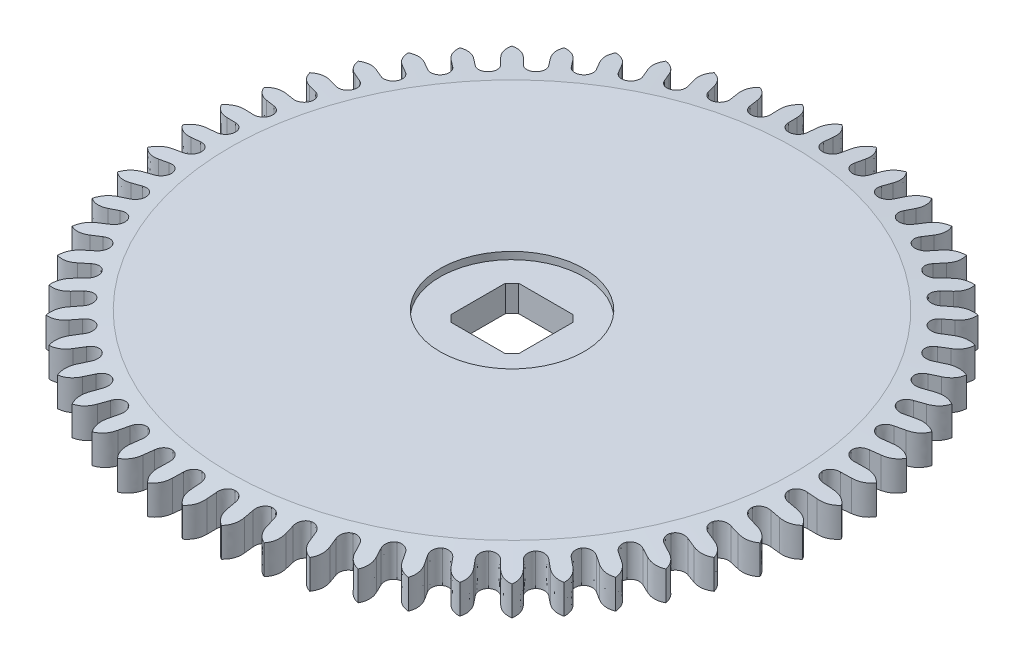
SolidWorks part; units mm, degrees
ref_plane "Alzado" through (0, 0, 0) normal (0, 0, 1) x (1, 0, 0)
ref_plane "Planta" through (0, 0, 0) normal (0, 1, 0) x (1, 0, 0)
ref_plane "Vista lateral" through (0, 0, 0) normal (1, 0, 0) x (0, 0, -1)
sketch "Sketch2" plane through (0, 0, 0) normal (0, 1, 0) x (1, 0, 0)
  circle A0 centre (0, 0) radius 6.875
  dimension "D1" = 13.75
extrude "Boss-Extrude2" add sketch "Sketch2" along normal blind 0.7
chamfer "Chamfer1" distance 0.09 distance2 1 1 edges at (0, 0.7, 6.875)
sketch "Sketch1" plane through (0, 0, 0) normal (0, 1, 0) x (1, 0, 0)
  line L0 (0, -1000) -> (0, 49000) construction
  line L1 (0, 0) -> (2803.5223, 49921.3408) construction
  line L2 (0.167, 6.5259) -> (0.167, 6.3258)
  line L3 (0.167, -994.7938) -> (0.167, 49005.2062) construction
  line L4 (-0.167, 6.5259) -> (-0.167, 6.3258)
  line L5 (0.5647, 6.5035) -> (0.5423, 6.3047)
  line L6 (0.8966, 6.4661) -> (0.8742, 6.2673)
  line L7 (1.2893, 6.3994) -> (1.2448, 6.2044)
  line L8 (1.615, 6.3251) -> (1.5704, 6.13)
  line L9 (1.9977, 6.2148) -> (1.9316, 6.026)
  line L10 (2.313, 6.1045) -> (2.2469, 5.9157)
  line L11 (2.681, 5.9521) -> (2.5942, 5.7718)
  line L12 (2.9819, 5.8071) -> (2.8951, 5.6269)
  line L13 (3.3306, 5.6145) -> (3.2241, 5.4451)
  line L14 (3.6134, 5.4368) -> (3.5069, 5.2674)
  line L15 (3.9382, 5.2062) -> (3.8135, 5.0498)
  line L16 (4.1994, 4.998) -> (4.0746, 4.8416)
  line L17 (4.4964, 4.7326) -> (4.3549, 4.5911)
  line L18 (4.7326, 4.4964) -> (4.5911, 4.3549)
  line L19 (4.998, 4.1994) -> (4.8416, 4.0746)
  line L20 (5.2062, 3.9382) -> (5.0498, 3.8135)
  line L21 (5.4368, 3.6134) -> (5.2674, 3.5069)
  line L22 (5.6145, 3.3306) -> (5.4451, 3.2241)
  line L23 (5.8071, 2.9819) -> (5.6269, 2.8951)
  line L24 (5.9521, 2.681) -> (5.7718, 2.5942)
  line L25 (6.1045, 2.313) -> (5.9157, 2.2469)
  line L26 (6.2148, 1.9977) -> (6.026, 1.9316)
  line L27 (6.3251, 1.615) -> (6.13, 1.5704)
  line L28 (6.3994, 1.2893) -> (6.2044, 1.2448)
  line L29 (6.4661, 0.8966) -> (6.2673, 0.8742)
  line L30 (6.5035, 0.5647) -> (6.3047, 0.5423)
  line L31 (6.5259, 0.167) -> (6.3258, 0.167)
  line L32 (6.5259, -0.167) -> (6.3258, -0.167)
  line L33 (6.5035, -0.5647) -> (6.3047, -0.5423)
  line L34 (6.4661, -0.8966) -> (6.2673, -0.8742)
  line L35 (6.3994, -1.2893) -> (6.2044, -1.2448)
  line L36 (6.3251, -1.615) -> (6.13, -1.5704)
  line L37 (6.2148, -1.9977) -> (6.026, -1.9316)
  line L38 (6.1045, -2.313) -> (5.9157, -2.2469)
  line L39 (5.9521, -2.681) -> (5.7718, -2.5942)
  line L40 (5.8071, -2.9819) -> (5.6269, -2.8951)
  line L41 (5.6145, -3.3306) -> (5.4451, -3.2241)
  line L42 (5.4368, -3.6134) -> (5.2674, -3.5069)
  line L43 (5.2062, -3.9382) -> (5.0498, -3.8135)
  line L44 (4.998, -4.1994) -> (4.8416, -4.0746)
  line L45 (4.7326, -4.4964) -> (4.5911, -4.3549)
  line L46 (4.4964, -4.7326) -> (4.3549, -4.5911)
  line L47 (4.1994, -4.998) -> (4.0746, -4.8416)
  line L48 (3.9382, -5.2062) -> (3.8135, -5.0498)
  line L49 (3.6134, -5.4368) -> (3.5069, -5.2674)
  line L50 (3.3306, -5.6145) -> (3.2241, -5.4451)
  line L51 (2.9819, -5.8071) -> (2.8951, -5.6269)
  line L52 (2.681, -5.9521) -> (2.5942, -5.7718)
  line L53 (2.313, -6.1045) -> (2.2469, -5.9157)
  line L54 (1.9977, -6.2148) -> (1.9316, -6.026)
  line L55 (1.615, -6.3251) -> (1.5704, -6.13)
  line L56 (1.2893, -6.3994) -> (1.2448, -6.2044)
  line L57 (0.8966, -6.4661) -> (0.8742, -6.2673)
  line L58 (0.5647, -6.5035) -> (0.5423, -6.3047)
  line L59 (0.167, -6.5259) -> (0.167, -6.3258)
  line L60 (-0.167, -6.5259) -> (-0.167, -6.3258)
  line L61 (-0.5647, -6.5035) -> (-0.5423, -6.3047)
  line L62 (-0.8966, -6.4661) -> (-0.8742, -6.2673)
  line L63 (-1.2893, -6.3994) -> (-1.2448, -6.2044)
  line L64 (-1.615, -6.3251) -> (-1.5704, -6.13)
  line L65 (-1.9977, -6.2148) -> (-1.9316, -6.026)
  line L66 (-2.313, -6.1045) -> (-2.2469, -5.9157)
  line L67 (-2.681, -5.9521) -> (-2.5942, -5.7718)
  line L68 (-2.9819, -5.8071) -> (-2.8951, -5.6269)
  line L69 (-3.3306, -5.6145) -> (-3.2241, -5.4451)
  line L70 (-3.6134, -5.4368) -> (-3.5069, -5.2674)
  line L71 (-3.9382, -5.2062) -> (-3.8135, -5.0498)
  line L72 (-4.1994, -4.998) -> (-4.0746, -4.8416)
  line L73 (-4.4964, -4.7326) -> (-4.3549, -4.5911)
  line L74 (-4.7326, -4.4964) -> (-4.5911, -4.3549)
  line L75 (-4.998, -4.1994) -> (-4.8416, -4.0746)
  line L76 (-5.2062, -3.9382) -> (-5.0498, -3.8135)
  line L77 (-5.4368, -3.6134) -> (-5.2674, -3.5069)
  line L78 (-5.6145, -3.3306) -> (-5.4451, -3.2241)
  line L79 (-5.8071, -2.9819) -> (-5.6269, -2.8951)
  line L80 (-5.9521, -2.681) -> (-5.7718, -2.5942)
  line L81 (-6.1045, -2.313) -> (-5.9157, -2.2469)
  line L82 (-6.2148, -1.9977) -> (-6.026, -1.9316)
  line L83 (-6.3251, -1.615) -> (-6.13, -1.5704)
  line L84 (-6.3994, -1.2893) -> (-6.2044, -1.2448)
  line L85 (-6.4661, -0.8966) -> (-6.2673, -0.8742)
  line L86 (-6.5035, -0.5647) -> (-6.3047, -0.5423)
  line L87 (-6.5259, -0.167) -> (-6.3258, -0.167)
  line L88 (-6.5259, 0.167) -> (-6.3258, 0.167)
  line L89 (-6.5035, 0.5647) -> (-6.3047, 0.5423)
  line L90 (-6.4661, 0.8966) -> (-6.2673, 0.8742)
  line L91 (-6.3994, 1.2893) -> (-6.2044, 1.2448)
  line L92 (-6.3251, 1.615) -> (-6.13, 1.5704)
  line L93 (-6.2148, 1.9977) -> (-6.026, 1.9316)
  line L94 (-6.1045, 2.313) -> (-5.9157, 2.2469)
  line L95 (-5.9521, 2.681) -> (-5.7718, 2.5942)
  line L96 (-5.8071, 2.9819) -> (-5.6269, 2.8951)
  line L97 (-5.6145, 3.3306) -> (-5.4451, 3.2241)
  line L98 (-5.4368, 3.6134) -> (-5.2674, 3.5069)
  line L99 (-5.2062, 3.9382) -> (-5.0498, 3.8135)
  line L100 (-4.998, 4.1994) -> (-4.8416, 4.0746)
  line L101 (-4.7326, 4.4964) -> (-4.5911, 4.3549)
  line L102 (-4.4964, 4.7326) -> (-4.3549, 4.5911)
  line L103 (-4.1994, 4.998) -> (-4.0746, 4.8416)
  line L104 (-3.9382, 5.2062) -> (-3.8135, 5.0498)
  line L105 (-3.6134, 5.4368) -> (-3.5069, 5.2674)
  line L106 (-3.3306, 5.6145) -> (-3.2241, 5.4451)
  line L107 (-2.9819, 5.8071) -> (-2.8951, 5.6269)
  line L108 (-2.681, 5.9521) -> (-2.5942, 5.7718)
  line L109 (-2.313, 6.1045) -> (-2.2469, 5.9157)
  line L110 (-1.9977, 6.2148) -> (-1.9316, 6.026)
  line L111 (-1.615, 6.3251) -> (-1.5704, 6.13)
  line L112 (-1.2893, 6.3994) -> (-1.2448, 6.2044)
  line L113 (-0.8966, 6.4661) -> (-0.8742, 6.2673)
  line L114 (-0.5647, 6.5035) -> (-0.5423, 6.3047)
  circle A0 centre (0, 0) radius 6.875 construction
  circle A1 centre (0, 0) radius 6.125 construction
  circle A2 centre (0, 0) radius 6.328 construction
  circle A3 centre (0, 0) radius 6.528 construction
  parabola Q0 (0, 6.875) -> (0.167, 6.5259) focus (-0.047, 6.652) apex (0.118, 6.742)
  parabola Q1 (0, 6.875) -> (-0.167, 6.5259) focus (0.047, 6.652) apex (-0.118, 6.742)
  parabola Q2 (0.7686, 6.8218) -> (0.5647, 6.5035) focus (0.7904, 6.595) apex (0.6364, 6.7028)
  parabola Q3 (0.7686, 6.8218) -> (0.8966, 6.4661) focus (0.697, 6.6055) apex (0.871, 6.6764)
  parabola Q4 (1.5276, 6.6929) -> (1.2893, 6.3994) focus (1.5238, 6.465) apex (1.3829, 6.5894)
  parabola Q5 (1.5276, 6.6929) -> (1.615, 6.3251) focus (1.4322, 6.4859) apex (1.6131, 6.5369)
  parabola Q6 (2.2674, 6.4798) -> (1.9977, 6.2148) focus (2.2381, 6.2537) apex (2.112, 6.3931)
  parabola Q7 (2.2674, 6.4798) -> (2.313, 6.1045) focus (2.1494, 6.2848) apex (2.3348, 6.3151)
  parabola Q8 (2.9786, 6.1852) -> (2.681, 5.9521) focus (2.9242, 5.9638) apex (2.8145, 6.1164)
  parabola Q9 (2.9786, 6.1852) -> (2.9819, 5.8071) focus (2.8395, 6.0046) apex (3.0272, 6.014)
  parabola Q10 (3.6524, 5.8128) -> (3.3306, 5.6145) focus (3.5736, 5.5989) apex (3.4816, 5.7629)
  parabola Q11 (3.6524, 5.8128) -> (3.6134, 5.4368) focus (3.494, 5.6489) apex (3.6815, 5.6373)
  parabola Q12 (4.2803, 5.3673) -> (3.9382, 5.2062) focus (4.178, 5.1636) apex (4.105, 5.3368)
  parabola Q13 (4.2803, 5.3673) -> (4.1994, 4.998) focus (4.1045, 5.2222) apex (4.2895, 5.1896)
  parabola Q14 (4.8543, 4.8543) -> (4.4964, 4.7326) focus (4.7298, 4.6634) apex (4.6767, 4.8436)
  parabola Q15 (4.8543, 4.8543) -> (4.7326, 4.4964) focus (4.6634, 4.7298) apex (4.8436, 4.6767)
  parabola Q16 (5.3673, 4.2803) -> (4.998, 4.1994) focus (5.2222, 4.1045) apex (5.1896, 4.2895)
  parabola Q17 (5.3673, 4.2803) -> (5.2062, 3.9382) focus (5.1636, 4.178) apex (5.3368, 4.105)
  parabola Q18 (5.8128, 3.6524) -> (5.4368, 3.6134) focus (5.6489, 3.494) apex (5.6373, 3.6815)
  parabola Q19 (5.8128, 3.6524) -> (5.6145, 3.3306) focus (5.5989, 3.5736) apex (5.7629, 3.4816)
  parabola Q20 (6.1852, 2.9786) -> (5.8071, 2.9819) focus (6.0046, 2.8395) apex (6.014, 3.0272)
  parabola Q21 (6.1852, 2.9786) -> (5.9521, 2.681) focus (5.9638, 2.9242) apex (6.1164, 2.8145)
  parabola Q22 (6.4798, 2.2674) -> (6.1045, 2.313) focus (6.2848, 2.1494) apex (6.3151, 2.3348)
  parabola Q23 (6.4798, 2.2674) -> (6.2148, 1.9977) focus (6.2537, 2.2381) apex (6.3931, 2.112)
  parabola Q24 (6.6929, 1.5276) -> (6.3251, 1.615) focus (6.4859, 1.4322) apex (6.5369, 1.6131)
  parabola Q25 (6.6929, 1.5276) -> (6.3994, 1.2893) focus (6.465, 1.5238) apex (6.5894, 1.3829)
  parabola Q26 (6.8218, 0.7686) -> (6.4661, 0.8966) focus (6.6055, 0.697) apex (6.6764, 0.871)
  parabola Q27 (6.8218, 0.7686) -> (6.5035, 0.5647) focus (6.595, 0.7904) apex (6.7028, 0.6364)
  parabola Q28 (6.865, 0) -> (6.5259, 0.167) focus (6.642, -0.047) apex (6.7319, 0.118)
  parabola Q29 (6.865, 0) -> (6.5259, -0.167) focus (6.642, 0.047) apex (6.7319, -0.118)
  parabola Q30 (6.8218, -0.7686) -> (6.5035, -0.5647) focus (6.595, -0.7904) apex (6.7028, -0.6364)
  parabola Q31 (6.8218, -0.7686) -> (6.4661, -0.8966) focus (6.6055, -0.697) apex (6.6764, -0.871)
  parabola Q32 (6.6929, -1.5276) -> (6.3994, -1.2893) focus (6.465, -1.5238) apex (6.5894, -1.3829)
  parabola Q33 (6.6929, -1.5276) -> (6.3251, -1.615) focus (6.4859, -1.4322) apex (6.5369, -1.6131)
  parabola Q34 (6.4798, -2.2674) -> (6.2148, -1.9977) focus (6.2537, -2.2381) apex (6.3931, -2.112)
  parabola Q35 (6.4798, -2.2674) -> (6.1045, -2.313) focus (6.2848, -2.1494) apex (6.3151, -2.3348)
  parabola Q36 (6.1852, -2.9786) -> (5.9521, -2.681) focus (5.9638, -2.9242) apex (6.1164, -2.8145)
  parabola Q37 (6.1852, -2.9786) -> (5.8071, -2.9819) focus (6.0046, -2.8395) apex (6.014, -3.0272)
  parabola Q38 (5.8128, -3.6524) -> (5.6145, -3.3306) focus (5.5989, -3.5736) apex (5.7629, -3.4816)
  parabola Q39 (5.8128, -3.6524) -> (5.4368, -3.6134) focus (5.6489, -3.494) apex (5.6373, -3.6815)
  parabola Q40 (5.3673, -4.2803) -> (5.2062, -3.9382) focus (5.1636, -4.178) apex (5.3368, -4.105)
  parabola Q41 (5.3673, -4.2803) -> (4.998, -4.1994) focus (5.2222, -4.1045) apex (5.1896, -4.2895)
  parabola Q42 (4.8543, -4.8543) -> (4.7326, -4.4964) focus (4.6634, -4.7298) apex (4.8436, -4.6767)
  parabola Q43 (4.8543, -4.8543) -> (4.4964, -4.7326) focus (4.7298, -4.6634) apex (4.6767, -4.8436)
  parabola Q44 (4.2803, -5.3673) -> (4.1994, -4.998) focus (4.1045, -5.2222) apex (4.2895, -5.1896)
  parabola Q45 (4.2803, -5.3673) -> (3.9382, -5.2062) focus (4.178, -5.1636) apex (4.105, -5.3368)
  parabola Q46 (3.6524, -5.8128) -> (3.6134, -5.4368) focus (3.494, -5.6489) apex (3.6815, -5.6373)
  parabola Q47 (3.6524, -5.8128) -> (3.3306, -5.6145) focus (3.5736, -5.5989) apex (3.4816, -5.7629)
  parabola Q48 (2.9786, -6.1852) -> (2.9819, -5.8071) focus (2.8395, -6.0046) apex (3.0272, -6.014)
  parabola Q49 (2.9786, -6.1852) -> (2.681, -5.9521) focus (2.9242, -5.9638) apex (2.8145, -6.1164)
  parabola Q50 (2.2674, -6.4798) -> (2.313, -6.1045) focus (2.1494, -6.2848) apex (2.3348, -6.3151)
  parabola Q51 (2.2674, -6.4798) -> (1.9977, -6.2148) focus (2.2381, -6.2537) apex (2.112, -6.3931)
  parabola Q52 (1.5276, -6.6929) -> (1.615, -6.3251) focus (1.4322, -6.4859) apex (1.6131, -6.5369)
  parabola Q53 (1.5276, -6.6929) -> (1.2893, -6.3994) focus (1.5238, -6.465) apex (1.3829, -6.5894)
  parabola Q54 (0.7686, -6.8218) -> (0.8966, -6.4661) focus (0.697, -6.6055) apex (0.871, -6.6764)
  parabola Q55 (0.7686, -6.8218) -> (0.5647, -6.5035) focus (0.7904, -6.595) apex (0.6364, -6.7028)
  parabola Q56 (0, -6.865) -> (0.167, -6.5259) focus (-0.047, -6.642) apex (0.118, -6.7319)
  parabola Q57 (0, -6.865) -> (-0.167, -6.5259) focus (0.047, -6.642) apex (-0.118, -6.7319)
  parabola Q58 (-0.7686, -6.8218) -> (-0.5647, -6.5035) focus (-0.7904, -6.595) apex (-0.6364, -6.7028)
  parabola Q59 (-0.7686, -6.8218) -> (-0.8966, -6.4661) focus (-0.697, -6.6055) apex (-0.871, -6.6764)
  parabola Q60 (-1.5276, -6.6929) -> (-1.2893, -6.3994) focus (-1.5238, -6.465) apex (-1.3829, -6.5894)
  parabola Q61 (-1.5276, -6.6929) -> (-1.615, -6.3251) focus (-1.4322, -6.4859) apex (-1.6131, -6.5369)
  parabola Q62 (-2.2674, -6.4798) -> (-1.9977, -6.2148) focus (-2.2381, -6.2537) apex (-2.112, -6.3931)
  parabola Q63 (-2.2674, -6.4798) -> (-2.313, -6.1045) focus (-2.1494, -6.2848) apex (-2.3348, -6.3151)
  parabola Q64 (-2.9786, -6.1852) -> (-2.681, -5.9521) focus (-2.9242, -5.9638) apex (-2.8145, -6.1164)
  parabola Q65 (-2.9786, -6.1852) -> (-2.9819, -5.8071) focus (-2.8395, -6.0046) apex (-3.0272, -6.014)
  parabola Q66 (-3.6524, -5.8128) -> (-3.3306, -5.6145) focus (-3.5736, -5.5989) apex (-3.4816, -5.7629)
  parabola Q67 (-3.6524, -5.8128) -> (-3.6134, -5.4368) focus (-3.494, -5.6489) apex (-3.6815, -5.6373)
  parabola Q68 (-4.2803, -5.3673) -> (-3.9382, -5.2062) focus (-4.178, -5.1636) apex (-4.105, -5.3368)
  parabola Q69 (-4.2803, -5.3673) -> (-4.1994, -4.998) focus (-4.1045, -5.2222) apex (-4.2895, -5.1896)
  parabola Q70 (-4.8543, -4.8543) -> (-4.4964, -4.7326) focus (-4.7298, -4.6634) apex (-4.6767, -4.8436)
  parabola Q71 (-4.8543, -4.8543) -> (-4.7326, -4.4964) focus (-4.6634, -4.7298) apex (-4.8436, -4.6767)
  parabola Q72 (-5.3673, -4.2803) -> (-4.998, -4.1994) focus (-5.2222, -4.1045) apex (-5.1896, -4.2895)
  parabola Q73 (-5.3673, -4.2803) -> (-5.2062, -3.9382) focus (-5.1636, -4.178) apex (-5.3368, -4.105)
  parabola Q74 (-5.8128, -3.6524) -> (-5.4368, -3.6134) focus (-5.6489, -3.494) apex (-5.6373, -3.6815)
  parabola Q75 (-5.8128, -3.6524) -> (-5.6145, -3.3306) focus (-5.5989, -3.5736) apex (-5.7629, -3.4816)
  parabola Q76 (-6.1852, -2.9786) -> (-5.8071, -2.9819) focus (-6.0046, -2.8395) apex (-6.014, -3.0272)
  parabola Q77 (-6.1852, -2.9786) -> (-5.9521, -2.681) focus (-5.9638, -2.9242) apex (-6.1164, -2.8145)
  parabola Q78 (-6.4798, -2.2674) -> (-6.1045, -2.313) focus (-6.2848, -2.1494) apex (-6.3151, -2.3348)
  parabola Q79 (-6.4798, -2.2674) -> (-6.2148, -1.9977) focus (-6.2537, -2.2381) apex (-6.3931, -2.112)
  parabola Q80 (-6.6929, -1.5276) -> (-6.3251, -1.615) focus (-6.4859, -1.4322) apex (-6.5369, -1.6131)
  parabola Q81 (-6.6929, -1.5276) -> (-6.3994, -1.2893) focus (-6.465, -1.5238) apex (-6.5894, -1.3829)
  parabola Q82 (-6.8218, -0.7686) -> (-6.4661, -0.8966) focus (-6.6055, -0.697) apex (-6.6764, -0.871)
  parabola Q83 (-6.8218, -0.7686) -> (-6.5035, -0.5647) focus (-6.595, -0.7904) apex (-6.7028, -0.6364)
  parabola Q84 (-6.865, 0) -> (-6.5259, -0.167) focus (-6.642, 0.047) apex (-6.7319, -0.118)
  parabola Q85 (-6.865, 0) -> (-6.5259, 0.167) focus (-6.642, -0.047) apex (-6.7319, 0.118)
  parabola Q86 (-6.8218, 0.7686) -> (-6.5035, 0.5647) focus (-6.595, 0.7904) apex (-6.7028, 0.6364)
  parabola Q87 (-6.8218, 0.7686) -> (-6.4661, 0.8966) focus (-6.6055, 0.697) apex (-6.6764, 0.871)
  parabola Q88 (-6.6929, 1.5276) -> (-6.3994, 1.2893) focus (-6.465, 1.5238) apex (-6.5894, 1.3829)
  parabola Q89 (-6.6929, 1.5276) -> (-6.3251, 1.615) focus (-6.4859, 1.4322) apex (-6.5369, 1.6131)
  parabola Q90 (-6.4798, 2.2674) -> (-6.2148, 1.9977) focus (-6.2537, 2.2381) apex (-6.3931, 2.112)
  parabola Q91 (-6.4798, 2.2674) -> (-6.1045, 2.313) focus (-6.2848, 2.1494) apex (-6.3151, 2.3348)
  parabola Q92 (-6.1852, 2.9786) -> (-5.9521, 2.681) focus (-5.9638, 2.9242) apex (-6.1164, 2.8145)
  parabola Q93 (-6.1852, 2.9786) -> (-5.8071, 2.9819) focus (-6.0046, 2.8395) apex (-6.014, 3.0272)
  parabola Q94 (-5.8128, 3.6524) -> (-5.6145, 3.3306) focus (-5.5989, 3.5736) apex (-5.7629, 3.4816)
  parabola Q95 (-5.8128, 3.6524) -> (-5.4368, 3.6134) focus (-5.6489, 3.494) apex (-5.6373, 3.6815)
  parabola Q96 (-5.3673, 4.2803) -> (-5.2062, 3.9382) focus (-5.1636, 4.178) apex (-5.3368, 4.105)
  parabola Q97 (-5.3673, 4.2803) -> (-4.998, 4.1994) focus (-5.2222, 4.1045) apex (-5.1896, 4.2895)
  parabola Q98 (-4.8543, 4.8543) -> (-4.7326, 4.4964) focus (-4.6634, 4.7298) apex (-4.8436, 4.6767)
  parabola Q99 (-4.8543, 4.8543) -> (-4.4964, 4.7326) focus (-4.7298, 4.6634) apex (-4.6767, 4.8436)
  parabola Q100 (-4.2803, 5.3673) -> (-4.1994, 4.998) focus (-4.1045, 5.2222) apex (-4.2895, 5.1896)
  parabola Q101 (-4.2803, 5.3673) -> (-3.9382, 5.2062) focus (-4.178, 5.1636) apex (-4.105, 5.3368)
  parabola Q102 (-3.6524, 5.8128) -> (-3.6134, 5.4368) focus (-3.494, 5.6489) apex (-3.6815, 5.6373)
  parabola Q103 (-3.6524, 5.8128) -> (-3.3306, 5.6145) focus (-3.5736, 5.5989) apex (-3.4816, 5.7629)
  parabola Q104 (-2.9786, 6.1852) -> (-2.9819, 5.8071) focus (-2.8395, 6.0046) apex (-3.0272, 6.014)
  parabola Q105 (-2.9786, 6.1852) -> (-2.681, 5.9521) focus (-2.9242, 5.9638) apex (-2.8145, 6.1164)
  parabola Q106 (-2.2674, 6.4798) -> (-2.313, 6.1045) focus (-2.1494, 6.2848) apex (-2.3348, 6.3151)
  parabola Q107 (-2.2674, 6.4798) -> (-1.9977, 6.2148) focus (-2.2381, 6.2537) apex (-2.112, 6.3931)
  parabola Q108 (-1.5276, 6.6929) -> (-1.615, 6.3251) focus (-1.4322, 6.4859) apex (-1.6131, 6.5369)
  parabola Q109 (-1.5276, 6.6929) -> (-1.2893, 6.3994) focus (-1.5238, 6.465) apex (-1.3829, 6.5894)
  parabola Q110 (-0.7686, 6.8218) -> (-0.8966, 6.4661) focus (-0.697, 6.6055) apex (-0.871, 6.6764)
  parabola Q111 (-0.7686, 6.8218) -> (-0.5647, 6.5035) focus (-0.7904, 6.595) apex (-0.6364, 6.7028)
  spline S0 degree 3 poles (0.167, 6.3258) (0.1637, 6.2132) (0.2418, 6.1215) (0.3434, 6.1154) knots 0 0 0 0 1 1 1 1
  spline S1 degree 3 poles (-0.167, 6.3258) (-0.1637, 6.2132) (-0.2418, 6.1215) (-0.3434, 6.1154) knots 0 0 0 0 1 1 1 1
  spline S2 degree 3 poles (0.5423, 6.3047) (0.533, 6.1925) (0.4451, 6.1101) (0.3434, 6.1154) knots 0 0 0 0 1 1 1 1
  spline S3 degree 3 poles (0.8742, 6.2673) (0.8583, 6.1558) (0.9257, 6.056) (1.026, 6.0385) knots 0 0 0 0 1 1 1 1
  spline S4 degree 3 poles (1.2448, 6.2044) (1.223, 6.0938) (1.1264, 6.0219) (1.026, 6.0385) knots 0 0 0 0 1 1 1 1
  spline S5 degree 3 poles (1.5704, 6.13) (1.5422, 6.021) (1.5979, 5.9143) (1.6956, 5.8856) knots 0 0 0 0 1 1 1 1
  spline S6 degree 3 poles (1.9316, 6.026) (1.8976, 5.9186) (1.7936, 5.8579) (1.6956, 5.8856) knots 0 0 0 0 1 1 1 1
  spline S7 degree 3 poles (2.2469, 5.9157) (2.2066, 5.8105) (2.2501, 5.6982) (2.3439, 5.6588) knots 0 0 0 0 1 1 1 1
  spline S8 degree 3 poles (2.5942, 5.7718) (2.5483, 5.6689) (2.4382, 5.6202) (2.3439, 5.6588) knots 0 0 0 0 1 1 1 1
  spline S9 degree 3 poles (2.8951, 5.6269) (2.8433, 5.5269) (2.8739, 5.4104) (2.9628, 5.3607) knots 0 0 0 0 1 1 1 1
  spline S10 degree 3 poles (3.2241, 5.4451) (3.167, 5.348) (3.0521, 5.3119) (2.9628, 5.3607) knots 0 0 0 0 1 1 1 1
  spline S11 degree 3 poles (3.5069, 5.2674) (3.4442, 5.1738) (3.4616, 5.0546) (3.5444, 4.9953) knots 0 0 0 0 1 1 1 1
  spline S12 degree 3 poles (3.8135, 5.0498) (3.7459, 4.9597) (3.6277, 4.9368) (3.5444, 4.9953) knots 0 0 0 0 1 1 1 1
  spline S13 degree 3 poles (4.0746, 4.8416) (4.0019, 4.7556) (4.0058, 4.6352) (4.0814, 4.5671) knots 0 0 0 0 1 1 1 1
  spline S14 degree 3 poles (4.3549, 4.5911) (4.2776, 4.5092) (4.1576, 4.4996) (4.0814, 4.5671) knots 0 0 0 0 1 1 1 1
  spline S15 degree 3 poles (4.5911, 4.3549) (4.5092, 4.2776) (4.4996, 4.1576) (4.5671, 4.0814) knots 0 0 0 0 1 1 1 1
  spline S16 degree 3 poles (4.8416, 4.0746) (4.7556, 4.0019) (4.6352, 4.0058) (4.5671, 4.0814) knots 0 0 0 0 1 1 1 1
  spline S17 degree 3 poles (5.0498, 3.8135) (4.9597, 3.7459) (4.9368, 3.6277) (4.9953, 3.5444) knots 0 0 0 0 1 1 1 1
  spline S18 degree 3 poles (5.2674, 3.5069) (5.1738, 3.4442) (5.0546, 3.4616) (4.9953, 3.5444) knots 0 0 0 0 1 1 1 1
  spline S19 degree 3 poles (5.4451, 3.2241) (5.348, 3.167) (5.3119, 3.0521) (5.3607, 2.9628) knots 0 0 0 0 1 1 1 1
  spline S20 degree 3 poles (5.6269, 2.8951) (5.5269, 2.8433) (5.4104, 2.8739) (5.3607, 2.9628) knots 0 0 0 0 1 1 1 1
  spline S21 degree 3 poles (5.7718, 2.5942) (5.6689, 2.5483) (5.6202, 2.4382) (5.6588, 2.3439) knots 0 0 0 0 1 1 1 1
  spline S22 degree 3 poles (5.9157, 2.2469) (5.8105, 2.2066) (5.6982, 2.2501) (5.6588, 2.3439) knots 0 0 0 0 1 1 1 1
  spline S23 degree 3 poles (6.026, 1.9316) (5.9186, 1.8976) (5.8579, 1.7936) (5.8856, 1.6956) knots 0 0 0 0 1 1 1 1
  spline S24 degree 3 poles (6.13, 1.5704) (6.021, 1.5422) (5.9143, 1.5979) (5.8856, 1.6956) knots 0 0 0 0 1 1 1 1
  spline S25 degree 3 poles (6.2044, 1.2448) (6.0938, 1.223) (6.0219, 1.1264) (6.0385, 1.026) knots 0 0 0 0 1 1 1 1
  spline S26 degree 3 poles (6.2673, 0.8742) (6.1558, 0.8583) (6.056, 0.9257) (6.0385, 1.026) knots 0 0 0 0 1 1 1 1
  spline S27 degree 3 poles (6.3047, 0.5423) (6.1925, 0.533) (6.1101, 0.4451) (6.1154, 0.3434) knots 0 0 0 0 1 1 1 1
  spline S28 degree 3 poles (6.3258, 0.167) (6.2132, 0.1637) (6.1215, 0.2418) (6.1154, 0.3434) knots 0 0 0 0 1 1 1 1
  spline S29 degree 3 poles (6.3258, -0.167) (6.2132, -0.1637) (6.1215, -0.2418) (6.1154, -0.3434) knots 0 0 0 0 1 1 1 1
  spline S30 degree 3 poles (6.3047, -0.5423) (6.1925, -0.533) (6.1101, -0.4451) (6.1154, -0.3434) knots 0 0 0 0 1 1 1 1
  spline S31 degree 3 poles (6.2673, -0.8742) (6.1558, -0.8583) (6.056, -0.9257) (6.0385, -1.026) knots 0 0 0 0 1 1 1 1
  spline S32 degree 3 poles (6.2044, -1.2448) (6.0938, -1.223) (6.0219, -1.1264) (6.0385, -1.026) knots 0 0 0 0 1 1 1 1
  spline S33 degree 3 poles (6.13, -1.5704) (6.021, -1.5422) (5.9143, -1.5979) (5.8856, -1.6956) knots 0 0 0 0 1 1 1 1
  spline S34 degree 3 poles (6.026, -1.9316) (5.9186, -1.8976) (5.8579, -1.7936) (5.8856, -1.6956) knots 0 0 0 0 1 1 1 1
  spline S35 degree 3 poles (5.9157, -2.2469) (5.8105, -2.2066) (5.6982, -2.2501) (5.6588, -2.3439) knots 0 0 0 0 1 1 1 1
  spline S36 degree 3 poles (5.7718, -2.5942) (5.6689, -2.5483) (5.6202, -2.4382) (5.6588, -2.3439) knots 0 0 0 0 1 1 1 1
  spline S37 degree 3 poles (5.6269, -2.8951) (5.5269, -2.8433) (5.4104, -2.8739) (5.3607, -2.9628) knots 0 0 0 0 1 1 1 1
  spline S38 degree 3 poles (5.4451, -3.2241) (5.348, -3.167) (5.3119, -3.0521) (5.3607, -2.9628) knots 0 0 0 0 1 1 1 1
  spline S39 degree 3 poles (5.2674, -3.5069) (5.1738, -3.4442) (5.0546, -3.4616) (4.9953, -3.5444) knots 0 0 0 0 1 1 1 1
  spline S40 degree 3 poles (5.0498, -3.8135) (4.9597, -3.7459) (4.9368, -3.6277) (4.9953, -3.5444) knots 0 0 0 0 1 1 1 1
  spline S41 degree 3 poles (4.8416, -4.0746) (4.7556, -4.0019) (4.6352, -4.0058) (4.5671, -4.0814) knots 0 0 0 0 1 1 1 1
  spline S42 degree 3 poles (4.5911, -4.3549) (4.5092, -4.2776) (4.4996, -4.1576) (4.5671, -4.0814) knots 0 0 0 0 1 1 1 1
  spline S43 degree 3 poles (4.3549, -4.5911) (4.2776, -4.5092) (4.1576, -4.4996) (4.0814, -4.5671) knots 0 0 0 0 1 1 1 1
  spline S44 degree 3 poles (4.0746, -4.8416) (4.0019, -4.7556) (4.0058, -4.6352) (4.0814, -4.5671) knots 0 0 0 0 1 1 1 1
  spline S45 degree 3 poles (3.8135, -5.0498) (3.7459, -4.9597) (3.6277, -4.9368) (3.5444, -4.9953) knots 0 0 0 0 1 1 1 1
  spline S46 degree 3 poles (3.5069, -5.2674) (3.4442, -5.1738) (3.4616, -5.0546) (3.5444, -4.9953) knots 0 0 0 0 1 1 1 1
  spline S47 degree 3 poles (3.2241, -5.4451) (3.167, -5.348) (3.0521, -5.3119) (2.9628, -5.3607) knots 0 0 0 0 1 1 1 1
  spline S48 degree 3 poles (2.8951, -5.6269) (2.8433, -5.5269) (2.8739, -5.4104) (2.9628, -5.3607) knots 0 0 0 0 1 1 1 1
  spline S49 degree 3 poles (2.5942, -5.7718) (2.5483, -5.6689) (2.4382, -5.6202) (2.3439, -5.6588) knots 0 0 0 0 1 1 1 1
  spline S50 degree 3 poles (2.2469, -5.9157) (2.2066, -5.8105) (2.2501, -5.6982) (2.3439, -5.6588) knots 0 0 0 0 1 1 1 1
  spline S51 degree 3 poles (1.9316, -6.026) (1.8976, -5.9186) (1.7936, -5.8579) (1.6956, -5.8856) knots 0 0 0 0 1 1 1 1
  spline S52 degree 3 poles (1.5704, -6.13) (1.5422, -6.021) (1.5979, -5.9143) (1.6956, -5.8856) knots 0 0 0 0 1 1 1 1
  spline S53 degree 3 poles (1.2448, -6.2044) (1.223, -6.0938) (1.1264, -6.0219) (1.026, -6.0385) knots 0 0 0 0 1 1 1 1
  spline S54 degree 3 poles (0.8742, -6.2673) (0.8583, -6.1558) (0.9257, -6.056) (1.026, -6.0385) knots 0 0 0 0 1 1 1 1
  spline S55 degree 3 poles (0.5423, -6.3047) (0.533, -6.1925) (0.4451, -6.1101) (0.3434, -6.1154) knots 0 0 0 0 1 1 1 1
  spline S56 degree 3 poles (0.167, -6.3258) (0.1637, -6.2132) (0.2418, -6.1215) (0.3434, -6.1154) knots 0 0 0 0 1 1 1 1
  spline S57 degree 3 poles (-0.167, -6.3258) (-0.1637, -6.2132) (-0.2418, -6.1215) (-0.3434, -6.1154) knots 0 0 0 0 1 1 1 1
  spline S58 degree 3 poles (-0.5423, -6.3047) (-0.533, -6.1925) (-0.4451, -6.1101) (-0.3434, -6.1154) knots 0 0 0 0 1 1 1 1
  spline S59 degree 3 poles (-0.8742, -6.2673) (-0.8583, -6.1558) (-0.9257, -6.056) (-1.026, -6.0385) knots 0 0 0 0 1 1 1 1
  spline S60 degree 3 poles (-1.2448, -6.2044) (-1.223, -6.0938) (-1.1264, -6.0219) (-1.026, -6.0385) knots 0 0 0 0 1 1 1 1
  spline S61 degree 3 poles (-1.5704, -6.13) (-1.5422, -6.021) (-1.5979, -5.9143) (-1.6956, -5.8856) knots 0 0 0 0 1 1 1 1
  spline S62 degree 3 poles (-1.9316, -6.026) (-1.8976, -5.9186) (-1.7936, -5.8579) (-1.6956, -5.8856) knots 0 0 0 0 1 1 1 1
  spline S63 degree 3 poles (-2.2469, -5.9157) (-2.2066, -5.8105) (-2.2501, -5.6982) (-2.3439, -5.6588) knots 0 0 0 0 1 1 1 1
  spline S64 degree 3 poles (-2.5942, -5.7718) (-2.5483, -5.6689) (-2.4382, -5.6202) (-2.3439, -5.6588) knots 0 0 0 0 1 1 1 1
  spline S65 degree 3 poles (-2.8951, -5.6269) (-2.8433, -5.5269) (-2.8739, -5.4104) (-2.9628, -5.3607) knots 0 0 0 0 1 1 1 1
  spline S66 degree 3 poles (-3.2241, -5.4451) (-3.167, -5.348) (-3.0521, -5.3119) (-2.9628, -5.3607) knots 0 0 0 0 1 1 1 1
  spline S67 degree 3 poles (-3.5069, -5.2674) (-3.4442, -5.1738) (-3.4616, -5.0546) (-3.5444, -4.9953) knots 0 0 0 0 1 1 1 1
  spline S68 degree 3 poles (-3.8135, -5.0498) (-3.7459, -4.9597) (-3.6277, -4.9368) (-3.5444, -4.9953) knots 0 0 0 0 1 1 1 1
  spline S69 degree 3 poles (-4.0746, -4.8416) (-4.0019, -4.7556) (-4.0058, -4.6352) (-4.0814, -4.5671) knots 0 0 0 0 1 1 1 1
  spline S70 degree 3 poles (-4.3549, -4.5911) (-4.2776, -4.5092) (-4.1576, -4.4996) (-4.0814, -4.5671) knots 0 0 0 0 1 1 1 1
  spline S71 degree 3 poles (-4.5911, -4.3549) (-4.5092, -4.2776) (-4.4996, -4.1576) (-4.5671, -4.0814) knots 0 0 0 0 1 1 1 1
  spline S72 degree 3 poles (-4.8416, -4.0746) (-4.7556, -4.0019) (-4.6352, -4.0058) (-4.5671, -4.0814) knots 0 0 0 0 1 1 1 1
  spline S73 degree 3 poles (-5.0498, -3.8135) (-4.9597, -3.7459) (-4.9368, -3.6277) (-4.9953, -3.5444) knots 0 0 0 0 1 1 1 1
  spline S74 degree 3 poles (-5.2674, -3.5069) (-5.1738, -3.4442) (-5.0546, -3.4616) (-4.9953, -3.5444) knots 0 0 0 0 1 1 1 1
  spline S75 degree 3 poles (-5.4451, -3.2241) (-5.348, -3.167) (-5.3119, -3.0521) (-5.3607, -2.9628) knots 0 0 0 0 1 1 1 1
  spline S76 degree 3 poles (-5.6269, -2.8951) (-5.5269, -2.8433) (-5.4104, -2.8739) (-5.3607, -2.9628) knots 0 0 0 0 1 1 1 1
  spline S77 degree 3 poles (-5.7718, -2.5942) (-5.6689, -2.5483) (-5.6202, -2.4382) (-5.6588, -2.3439) knots 0 0 0 0 1 1 1 1
  spline S78 degree 3 poles (-5.9157, -2.2469) (-5.8105, -2.2066) (-5.6982, -2.2501) (-5.6588, -2.3439) knots 0 0 0 0 1 1 1 1
  spline S79 degree 3 poles (-6.026, -1.9316) (-5.9186, -1.8976) (-5.8579, -1.7936) (-5.8856, -1.6956) knots 0 0 0 0 1 1 1 1
  spline S80 degree 3 poles (-6.13, -1.5704) (-6.021, -1.5422) (-5.9143, -1.5979) (-5.8856, -1.6956) knots 0 0 0 0 1 1 1 1
  spline S81 degree 3 poles (-6.2044, -1.2448) (-6.0938, -1.223) (-6.0219, -1.1264) (-6.0385, -1.026) knots 0 0 0 0 1 1 1 1
  spline S82 degree 3 poles (-6.2673, -0.8742) (-6.1558, -0.8583) (-6.056, -0.9257) (-6.0385, -1.026) knots 0 0 0 0 1 1 1 1
  spline S83 degree 3 poles (-6.3047, -0.5423) (-6.1925, -0.533) (-6.1101, -0.4451) (-6.1154, -0.3434) knots 0 0 0 0 1 1 1 1
  spline S84 degree 3 poles (-6.3258, -0.167) (-6.2132, -0.1637) (-6.1215, -0.2418) (-6.1154, -0.3434) knots 0 0 0 0 1 1 1 1
  spline S85 degree 3 poles (-6.3258, 0.167) (-6.2132, 0.1637) (-6.1215, 0.2418) (-6.1154, 0.3434) knots 0 0 0 0 1 1 1 1
  spline S86 degree 3 poles (-6.3047, 0.5423) (-6.1925, 0.533) (-6.1101, 0.4451) (-6.1154, 0.3434) knots 0 0 0 0 1 1 1 1
  spline S87 degree 3 poles (-6.2673, 0.8742) (-6.1558, 0.8583) (-6.056, 0.9257) (-6.0385, 1.026) knots 0 0 0 0 1 1 1 1
  spline S88 degree 3 poles (-6.2044, 1.2448) (-6.0938, 1.223) (-6.0219, 1.1264) (-6.0385, 1.026) knots 0 0 0 0 1 1 1 1
  spline S89 degree 3 poles (-6.13, 1.5704) (-6.021, 1.5422) (-5.9143, 1.5979) (-5.8856, 1.6956) knots 0 0 0 0 1 1 1 1
  spline S90 degree 3 poles (-6.026, 1.9316) (-5.9186, 1.8976) (-5.8579, 1.7936) (-5.8856, 1.6956) knots 0 0 0 0 1 1 1 1
  spline S91 degree 3 poles (-5.9157, 2.2469) (-5.8105, 2.2066) (-5.6982, 2.2501) (-5.6588, 2.3439) knots 0 0 0 0 1 1 1 1
  spline S92 degree 3 poles (-5.7718, 2.5942) (-5.6689, 2.5483) (-5.6202, 2.4382) (-5.6588, 2.3439) knots 0 0 0 0 1 1 1 1
  spline S93 degree 3 poles (-5.6269, 2.8951) (-5.5269, 2.8433) (-5.4104, 2.8739) (-5.3607, 2.9628) knots 0 0 0 0 1 1 1 1
  spline S94 degree 3 poles (-5.4451, 3.2241) (-5.348, 3.167) (-5.3119, 3.0521) (-5.3607, 2.9628) knots 0 0 0 0 1 1 1 1
  spline S95 degree 3 poles (-5.2674, 3.5069) (-5.1738, 3.4442) (-5.0546, 3.4616) (-4.9953, 3.5444) knots 0 0 0 0 1 1 1 1
  spline S96 degree 3 poles (-5.0498, 3.8135) (-4.9597, 3.7459) (-4.9368, 3.6277) (-4.9953, 3.5444) knots 0 0 0 0 1 1 1 1
  spline S97 degree 3 poles (-4.8416, 4.0746) (-4.7556, 4.0019) (-4.6352, 4.0058) (-4.5671, 4.0814) knots 0 0 0 0 1 1 1 1
  spline S98 degree 3 poles (-4.5911, 4.3549) (-4.5092, 4.2776) (-4.4996, 4.1576) (-4.5671, 4.0814) knots 0 0 0 0 1 1 1 1
  spline S99 degree 3 poles (-4.3549, 4.5911) (-4.2776, 4.5092) (-4.1576, 4.4996) (-4.0814, 4.5671) knots 0 0 0 0 1 1 1 1
  spline S100 degree 3 poles (-4.0746, 4.8416) (-4.0019, 4.7556) (-4.0058, 4.6352) (-4.0814, 4.5671) knots 0 0 0 0 1 1 1 1
  spline S101 degree 3 poles (-3.8135, 5.0498) (-3.7459, 4.9597) (-3.6277, 4.9368) (-3.5444, 4.9953) knots 0 0 0 0 1 1 1 1
  spline S102 degree 3 poles (-3.5069, 5.2674) (-3.4442, 5.1738) (-3.4616, 5.0546) (-3.5444, 4.9953) knots 0 0 0 0 1 1 1 1
  spline S103 degree 3 poles (-3.2241, 5.4451) (-3.167, 5.348) (-3.0521, 5.3119) (-2.9628, 5.3607) knots 0 0 0 0 1 1 1 1
  spline S104 degree 3 poles (-2.8951, 5.6269) (-2.8433, 5.5269) (-2.8739, 5.4104) (-2.9628, 5.3607) knots 0 0 0 0 1 1 1 1
  spline S105 degree 3 poles (-2.5942, 5.7718) (-2.5483, 5.6689) (-2.4382, 5.6202) (-2.3439, 5.6588) knots 0 0 0 0 1 1 1 1
  spline S106 degree 3 poles (-2.2469, 5.9157) (-2.2066, 5.8105) (-2.2501, 5.6982) (-2.3439, 5.6588) knots 0 0 0 0 1 1 1 1
  spline S107 degree 3 poles (-1.9316, 6.026) (-1.8976, 5.9186) (-1.7936, 5.8579) (-1.6956, 5.8856) knots 0 0 0 0 1 1 1 1
  spline S108 degree 3 poles (-1.5704, 6.13) (-1.5422, 6.021) (-1.5979, 5.9143) (-1.6956, 5.8856) knots 0 0 0 0 1 1 1 1
  spline S109 degree 3 poles (-1.2448, 6.2044) (-1.223, 6.0938) (-1.1264, 6.0219) (-1.026, 6.0385) knots 0 0 0 0 1 1 1 1
  spline S110 degree 3 poles (-0.8742, 6.2673) (-0.8583, 6.1558) (-0.9257, 6.056) (-1.026, 6.0385) knots 0 0 0 0 1 1 1 1
  spline S111 degree 3 poles (-0.5423, 6.3047) (-0.533, 6.1925) (-0.4451, 6.1101) (-0.3434, 6.1154) knots 0 0 0 0 1 1 1 1
  point P4 (-0.047, 6.652)
  point P10 (0, 6.875)
  point P14 (0.167, 6.5259)
  point P15 (0.167, 6.3258)
  point P16 (0.3434, 6.1154)
  point P636 (0, 0)
  dimension "D1" = 13.75
  dimension "D2" = 12.25
  dimension "D6" = 12.656
  dimension "D7" = 13.056
  dimension "D3" = 3.214
  dimension "D4" = 0.167
  dimension "D5" = 0.047
  dimension "D8" = 0.223
  dimension "D9" = 56
extrude "Cut-Extrude1 (56 teeth)" cut sketch "Sketch1" along normal blind 0.7 flip side to cut
sketch "Sketch3" plane through (0, 0.7, 0) normal (0, 1, 0) x (1, 0, 0)
  circle A0 centre (0, 0) radius 1.5
  dimension "D1" = 3
extrude "Cut-Extrude2" cut sketch "Sketch3" against normal blind 0.15
sketch "Sketch4" plane through (0, 0, 0) normal (0, 1, 0) x (1, 0, 0)
  line L0 (-0.705, -1000.1025) -> (-0.705, 48999.8975) construction
  line L1 (0, -1000) -> (0, 49000) construction
  line L2 (0.705, -1000.0077) -> (0.705, 48999.9923) construction
  line L3 (-1000, 0) -> (49000, 0) construction
  line L4 (-1000, 0.705) -> (49000, 0.705) construction
  line L5 (-1000, -0.705) -> (49000, -0.705) construction
  line L6 (0.565, 0.705) -> (0.705, 0.565)
  line L7 (-0.565, 0.705) -> (0.565, 0.705)
  line L8 (-0.705, 0.565) -> (-0.705, -0.565)
  line L9 (-0.565, -0.705) -> (0.565, -0.705)
  line L10 (0.705, 0.565) -> (0.705, -0.565)
  line L11 (0.705, -0.565) -> (0.565, -0.705)
  line L12 (-0.705, -0.565) -> (-0.565, -0.705)
  line L13 (-0.565, 0.705) -> (-0.705, 0.565)
  point P12 (-0.705, 0.705)
  point P14 (0.705, -0.705)
  point P15 (-0.705, -0.705)
  point P16 (0.705, 0.705)
  dimension "D1" = 0.705
  dimension "D2" = 0.705
  dimension "D3" = 0.705
  dimension "D4" = 0.705
extrude "Cut-Extrude3" cut sketch "Sketch4" along normal up to next
